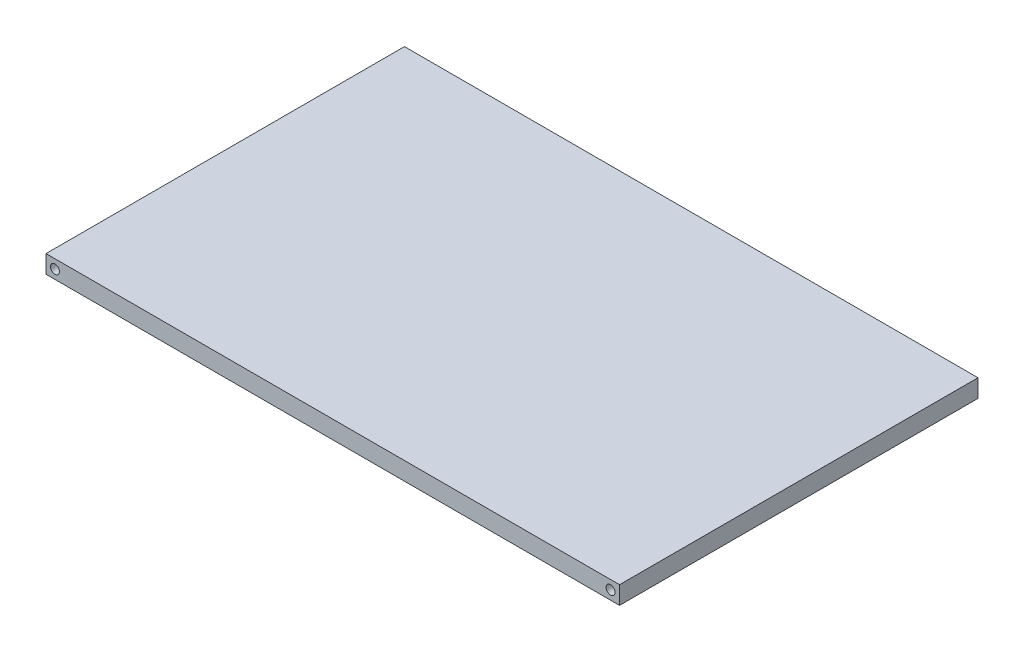
SolidWorks part; units mm, degrees
material "Acrylic (Medium-high impact)"
ref_plane "Front Plane" through (0, 0, 0) normal (0, 0, 1) x (1, 0, 0)
ref_plane "Top Plane" through (0, 0, 0) normal (0, 1, 0) x (1, 0, 0)
ref_plane "Right Plane" through (0, 0, 0) normal (1, 0, 0) x (0, 0, -1)
sketch "Sketch1" plane through (0, 0, 0) normal (0, 1, 0) x (1, 0, 0)
  line L1 (-42.2044, 20.6541) -> (59.3956, 20.6541)
  line L2 (-42.2044, 20.6541) -> (-42.2044, -42.8459)
  line L3 (-42.2044, -42.8459) -> (59.3956, -42.8459)
  line L4 (59.3956, 20.6541) -> (59.3956, -42.8459)
  dimension "D1" = 101.6
  dimension "D2" = 63.5
extrude "Boss-Extrude1" add sketch "Sketch1" along normal blind 3.175
sketch "Sketch2" plane through (0, 0, 42.8459) normal (0, 0, 1) x (1, 0, 0)
  line L0 (-42.2044, 3.175) -> (59.3956, 3.175) construction
  line L1 (-42.2044, 3.175) -> (-42.2044, 0) construction
  line L2 (59.3956, 3.175) -> (59.3956, 0) construction
  circle A0 centre (-40.6169, 1.5875) radius 0.7937
  circle A1 centre (57.8081, 1.5875) radius 0.7937
  dimension "D1" = 1.5875
  dimension "D4" = 1.5875
  dimension "D2" = 1.5875
  dimension "D3" = 1.5875
  dimension "D5" = 1.5875
  dimension "D6" = 1.5875
extrude "Cut-Extrude1" cut sketch "Sketch2" against normal blind 6.35
sketch "Sketch3" plane through (0, 0, -20.6541) normal (0, 0, -1) x (-1, 0, 0)
  line L0 (-59.3956, 3.175) -> (-59.3956, 0) construction
  line L1 (-59.3956, 0) -> (42.2044, 0) construction
  line L2 (42.2044, 3.175) -> (42.2044, 0) construction
  line L3 (-59.3956, 3.175) -> (42.2044, 3.175) construction
  circle A0 centre (-57.8081, 1.5875) radius 0.7937
  circle A1 centre (40.6169, 1.5875) radius 0.7937
  point P4 (-59.3956, 1.5875)
  point P9 (42.2044, 1.5875)
  dimension "D1" = 1.5875
  dimension "D3" = 1.5875
  dimension "D4" = 1.5875
  dimension "D2" = 1.5875
  dimension "D5" = 1.5875
  dimension "D6" = 1.5875
extrude "Cut-Extrude2" cut sketch "Sketch3" against normal blind 6.35
